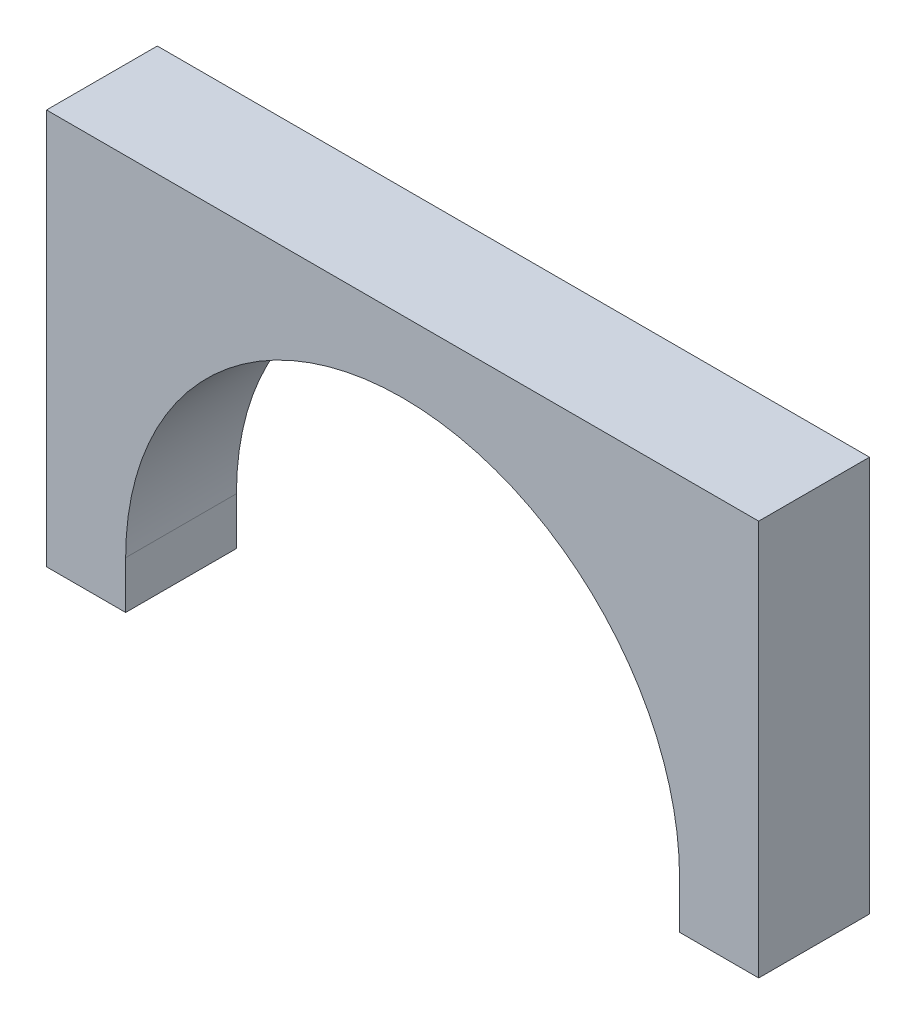
SolidWorks part; units mm, degrees
ref_plane "Front Plane" through (0, 0, 0) normal (0, 0, 1) x (1, 0, 0)
ref_plane "Top Plane" through (0, 0, 0) normal (0, 1, 0) x (1, 0, 0)
ref_plane "Right Plane" through (0, 0, 0) normal (1, 0, 0) x (0, 0, -1)
sketch "Sketch1" plane through (0, 0, 0) normal (0, 0, 1) x (1, 0, 0)
  line L0 (22.5, 0) -> (17.5, 0)
  line L1 (22.5, 0) -> (22.5, 25)
  line L2 (-22.5, 0) -> (-22.5, 25)
  line L3 (-22.5, 25) -> (22.5, 25)
  line L4 (-17.5, 0) -> (-17.5, 3)
  line L5 (-17.5, 0) -> (-22.5, 0)
  line L6 (17.5, 3) -> (17.5, 0)
  arc A0 (-17.5, 3) -> (17.5, 3) centre (0, 3) cw
  dimension "D1" = 45
  dimension "D2" = 22.5
  dimension "D3" = 25
  dimension "D4" = 3
  dimension "D5" = 3
  dimension "D6" = 5
  dimension "D7" = 5
extrude "Boss-Extrude1" add sketch "Sketch1" along normal blind 7
ref_plane "Plane1" through (22.5, 0, 0) normal (1, 0, 0) x (0, 0, -1)
